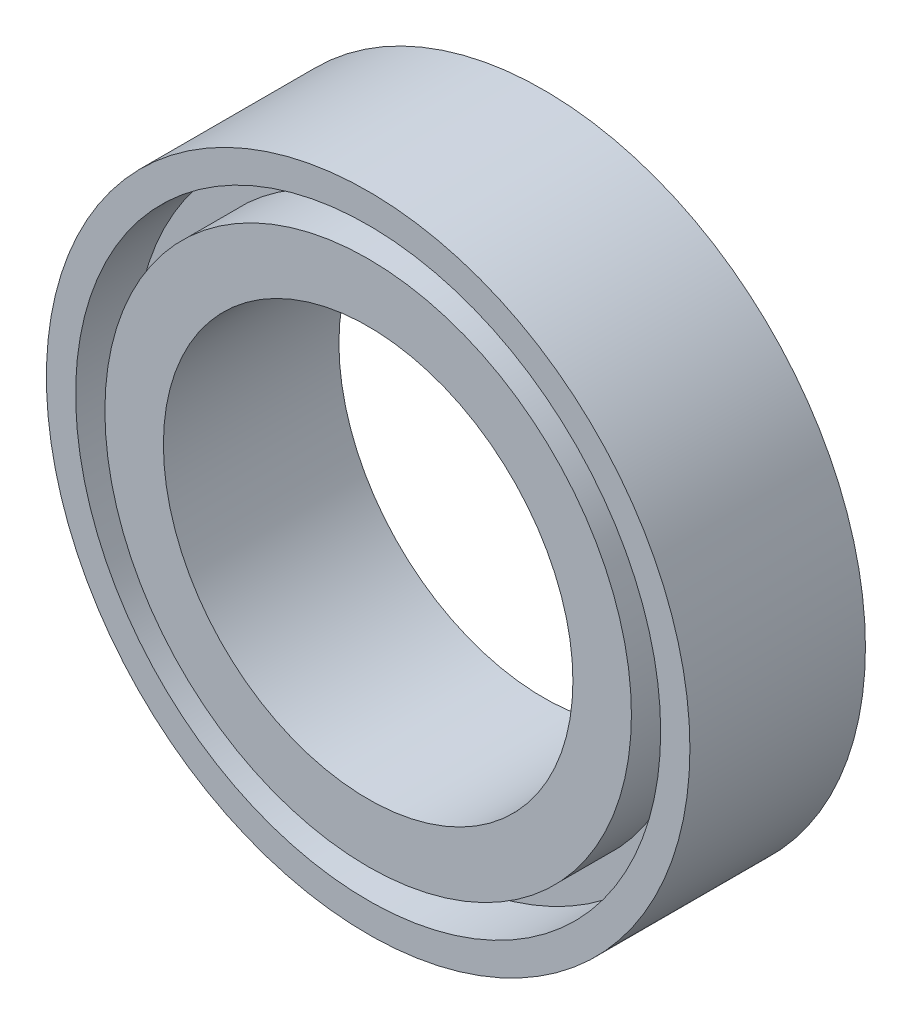
SolidWorks part; units mm, degrees
ref_plane "前视基准面" through (0, 0, 0) normal (0, 0, 1) x (1, 0, 0)
ref_plane "上视基准面" through (0, 0, 0) normal (0, 1, 0) x (1, 0, 0)
ref_plane "右视基准面" through (0, 0, 0) normal (1, 0, 0) x (0, 0, -1)
sketch "草图1" plane through (0, 0, 0) normal (0, 0, 1) x (1, 0, 0)
  circle A0 centre (0, 0) radius 3.5
  circle A1 centre (0, 0) radius 5.5
  dimension "D1" = 11
  dimension "D2" = 7
extrude "凸台-拉伸1" add sketch "草图1" along normal blind 3
sketch "草图2" plane through (0, 0, 3) normal (0, 0, 1) x (1, 0, 0)
  circle A0 centre (0, 0) radius 4.5
  circle A1 centre (0, 0) radius 5
  dimension "D1" = 9
  dimension "D2" = 10
extrude "切除-拉伸1" cut sketch "草图2" against normal blind 1
sketch "草图3" plane through (0, 0, 0) normal (0, 0, -1) x (-1, 0, 0)
  circle A0 centre (0, 0) radius 4.5
  circle A1 centre (0, 0) radius 5
  dimension "D1" = 9
  dimension "D2" = 10
extrude "切除-拉伸2" cut sketch "草图3" against normal blind 1
